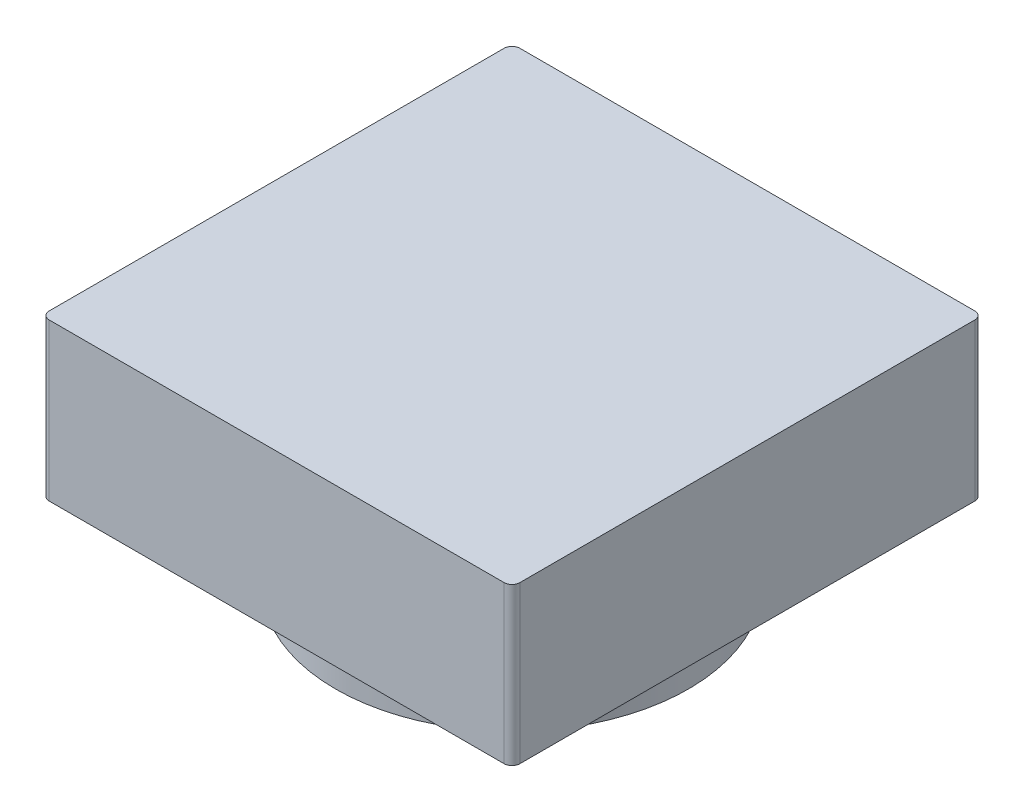
SolidWorks part; units mm, degrees
ref_plane "Front Plane" through (0, 0, 0) normal (0, 0, 1) x (1, 0, 0)
ref_plane "Top Plane" through (0, 0, 0) normal (0, 1, 0) x (1, 0, 0)
ref_plane "Right Plane" through (0, 0, 0) normal (1, 0, 0) x (0, 0, -1)
sketch "Sketch1" plane through (0, 0, 0) normal (0, 1, 0) x (1, 0, 0)
  circle A0 centre (0, 0) radius 22.5
  dimension "D1" = 45
extrude "Boss-Extrude1" add sketch "Sketch1" along normal blind 10
sketch "Sketch2" plane through (0, 10, 0) normal (0, 1, 0) x (1, 0, 0)
  line L1 (-29, 30) -> (29, 30)
  line L2 (-30, 29) -> (-30, -29)
  line L3 (-29, -30) -> (29, -30)
  line L4 (30, 29) -> (30, -29)
  line L5 (-30, 30) -> (30, -30) construction
  line L6 (-30, -30) -> (30, 30) construction
  arc A0 (-30, -29) -> (-29, -30) centre (-29, -29) ccw
  arc A1 (29, -30) -> (30, -29) centre (29, -29) ccw
  arc A2 (29, 30) -> (30, 29) centre (29, 29) cw
  arc A3 (-29, 30) -> (-30, 29) centre (-29, 29) ccw
  point P0 (0, 0)
  dimension "D1" = 60
  dimension "D3" = 1
  dimension "D2" = 60
extrude "Boss-Extrude2" add sketch "Sketch2" along normal blind 20
sketch "Sketch3" plane through (0, 0, 0) normal (0, -1, 0) x (1, 0, 0)
  line L0 (14.5514, 2.7786) -> (0, 30)
  line L1 (0, 30) -> (-14.5514, 2.7786)
  circle A0 centre (0, -5) radius 16.5
  circle A2 centre (0, 0) radius 22.5 construction
  circle A4 centre (0, 0) radius 21.5
  circle A5 centre (0, 0) radius 21.5
  dimension "D1" = 33
  dimension "D2" = 35
  dimension "D3" = 5
  dimension "D4" = 1
extrude "Cut-Extrude2" cut sketch "Sketch3" against normal blind 5 contours L0 A5 L1 A0 | A0
